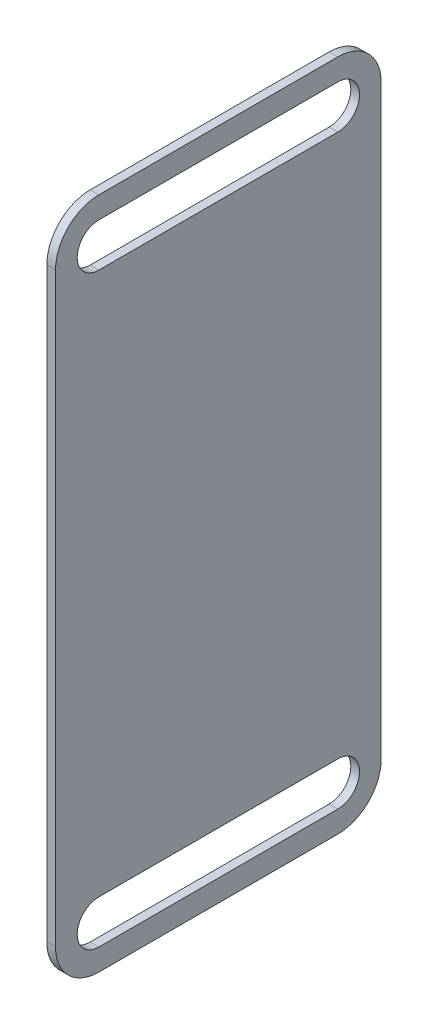
SolidWorks part; units mm, degrees
ref_plane "Front Plane" through (0, 0, 0) normal (0, 0, 1) x (1, 0, 0)
ref_plane "Top Plane" through (0, 0, 0) normal (0, 1, 0) x (1, 0, 0)
ref_plane "Right Plane" through (0, 0, 0) normal (1, 0, 0) x (0, 0, -1)
sketch "Sketch1" plane through (0, 0, 0) normal (1, 0, 0) x (0, 0, -1)
  line L0 (82.55, 12.7) -> (12.7, 12.7) construction
  line L1 (12.7, 0) -> (82.55, 0)
  line L2 (0, 12.7) -> (0, 184.15)
  line L3 (12.7, 196.85) -> (82.55, 196.85)
  line L4 (95.25, 12.7) -> (95.25, 184.15)
  line L9 (82.55, 6.35) -> (12.7, 6.35)
  line L10 (82.55, 19.05) -> (12.7, 19.05)
  line L11 (82.55, 184.15) -> (12.7, 184.15) construction
  line L12 (82.55, 177.8) -> (12.7, 177.8)
  line L13 (82.55, 190.5) -> (12.7, 190.5)
  arc A0 (12.7, 0) -> (0, 12.7) centre (12.7, 12.7) cw
  arc A1 (82.55, 0) -> (95.25, 12.7) centre (82.55, 12.7) ccw
  arc A2 (82.55, 196.85) -> (95.25, 184.15) centre (82.55, 184.15) cw
  arc A3 (0, 184.15) -> (12.7, 196.85) centre (12.7, 184.15) cw
  arc A4 (82.55, 6.35) -> (82.55, 19.05) centre (82.55, 12.7) ccw
  arc A5 (12.7, 19.05) -> (12.7, 6.35) centre (12.7, 12.7) ccw
  arc A6 (82.55, 177.8) -> (82.55, 190.5) centre (82.55, 184.15) ccw
  arc A7 (12.7, 190.5) -> (12.7, 177.8) centre (12.7, 184.15) ccw
  point P7 (0, 0)
  point P12 (95.25, 196.85)
  point P15 (0, 196.85)
  point P16 (47.625, 12.7)
  point P21 (47.625, 184.15)
  dimension "D3" = 12.7
  dimension "D4" = 6.35
  dimension "D5" = 6.35
  dimension "D1" = 196.85
  dimension "D2" = 95.25
extrude "Boss-Extrude1" add sketch "Sketch1" along normal blind 2.54
